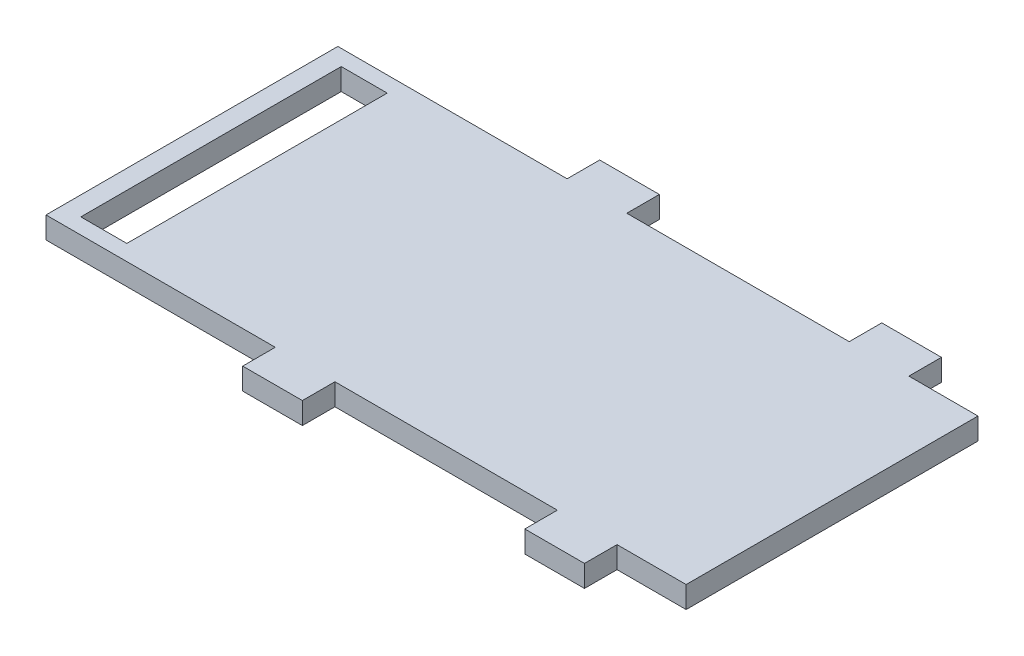
SolidWorks part; units mm, degrees
ref_plane "Front Plane" through (0, 0, 0) normal (0, 0, 1) x (1, 0, 0)
ref_plane "Top Plane" through (0, 0, 0) normal (0, 1, 0) x (1, 0, 0)
ref_plane "Right Plane" through (0, 0, 0) normal (1, 0, 0) x (0, 0, -1)
sketch "Sketch1" plane through (0, 0, 0) normal (0, 1, 0) x (1, 0, 0)
  line L1 (-50.7984, -5.3305) -> (-21.2984, -5.3305)
  line L2 (-50.7984, -5.3305) -> (-50.7984, -18.7805)
  line L3 (-50.7984, -18.7805) -> (-21.2984, -18.7805)
  line L4 (-21.2984, -5.3305) -> (-21.2984, -18.7805)
  dimension "D1" = 13.45
  dimension "D2" = 29.5
sketch "Sketch2" plane through (0, 0, 0) normal (0, 1, 0) x (1, 0, 0)
  line L0 (-50.7984, -5.3305) -> (-21.2984, -5.3305) construction
  line L1 (-40.2334, -5.3305) -> (-37.4834, -5.3305)
  line L2 (-40.2334, -5.3305) -> (-40.2334, -3.8305)
  line L3 (-40.2334, -3.8305) -> (-37.4834, -3.8305)
  line L4 (-37.4834, -5.3305) -> (-37.4834, -3.8305)
  line L5 (-50.7984, -5.3305) -> (-50.7984, -18.7805) construction
  line L6 (-21.2984, -5.3305) -> (-21.2984, -18.7805) construction
  line L7 (-50.7984, -18.7805) -> (-21.2984, -18.7805) construction
  line L8 (-40.2334, -18.7805) -> (-37.4834, -18.7805)
  line L9 (-40.2334, -18.7805) -> (-40.2334, -20.2805)
  line L10 (-40.2334, -20.2805) -> (-37.4834, -20.2805)
  line L11 (-37.4834, -18.7805) -> (-37.4834, -20.2805)
  line L12 (-27.2334, -5.3305) -> (-27.2334, -3.8305)
  line L13 (-27.2334, -3.8305) -> (-24.4834, -3.8305)
  line L14 (-24.4834, -5.3305) -> (-24.4834, -3.8305)
  line L15 (-27.2334, -5.3305) -> (-24.4834, -5.3305)
  line L16 (-27.2334, -18.7805) -> (-24.4834, -18.7805)
  line L17 (-24.4834, -18.7805) -> (-24.4834, -20.2805)
  line L18 (-27.2334, -20.2805) -> (-24.4834, -20.2805)
  line L19 (-27.2334, -18.7805) -> (-27.2334, -20.2805)
  dimension "D1" = 2.75
  dimension "D2" = 10.565
  dimension "D3" = 16.185
  dimension "D4" = 1.5
  dimension "D5" = 1.5
  dimension "D6" = 2.75
  dimension "D7" = 10.565
  dimension "D8" = 2
extrude "Boss-Extrude1" add sketch "Sketch1" along normal blind 1
extrude "Boss-Extrude2" add sketch "Sketch2" along normal blind 1
sketch "Sketch3" plane through (0, 0, 0) normal (0, -1, 0) x (-1, 0, 0)
  line L0 (50.7984, -18.7805) -> (21.2984, -18.7805) construction
  line L1 (49.9184, -18.0555) -> (47.7984, -18.0555)
  line L2 (49.9184, -18.0555) -> (49.9184, -6.0555)
  line L3 (49.9184, -6.0555) -> (47.7984, -6.0555)
  line L4 (47.7984, -18.0555) -> (47.7984, -6.0555)
  line L5 (50.7984, -5.3305) -> (21.2984, -5.3305) construction
  line L6 (50.7984, -5.3305) -> (50.7984, -18.7805) construction
  dimension "D1" = 2.12
  dimension "D2" = 12
  dimension "D3" = 0.725
  dimension "D4" = 0.725
  dimension "D5" = 0.88
extrude "adapter_PCB_hole" cut sketch "Sketch3" against normal blind 1
